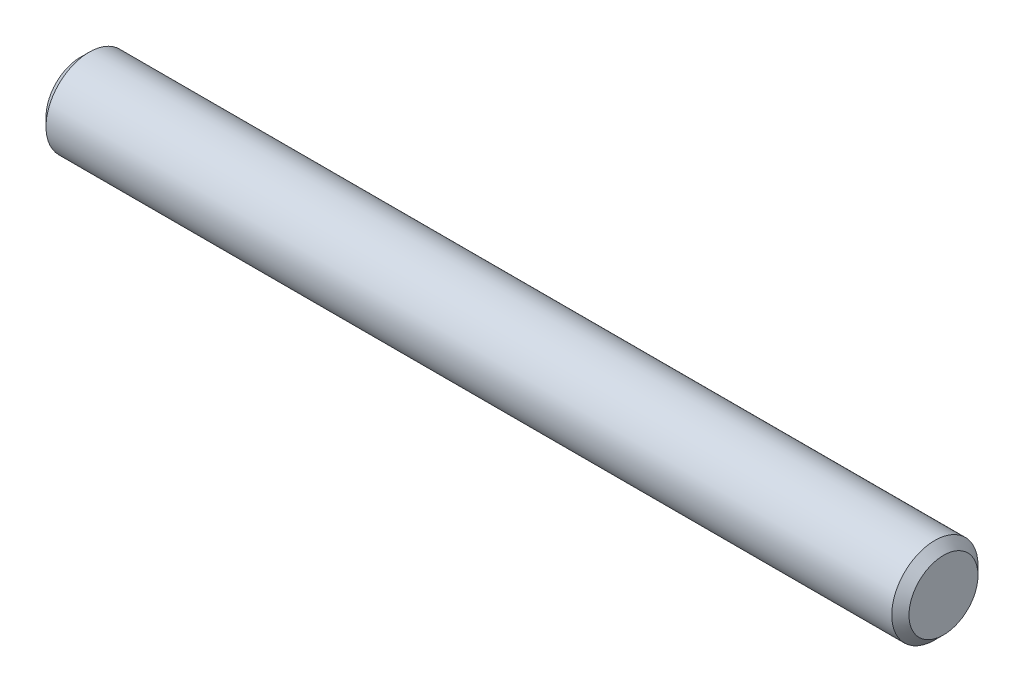
SolidWorks part; units mm, degrees
ref_plane "Front Plane" through (0, 0, 0) normal (0, 0, 1) x (1, 0, 0)
ref_plane "Top Plane" through (0, 0, 0) normal (0, 1, 0) x (1, 0, 0)
ref_plane "Right Plane" through (0, 0, 0) normal (1, 0, 0) x (0, 0, -1)
sketch "Sketch1" plane through (0, 0, 0) normal (0, 0, 1) x (1, 0, 0)
  line L0 (-31.75, 0) -> (31.75, 0) construction
  line L1 (-31.75, 3.175) -> (-31.75, -3.175) construction
  line L2 (31.75, 3.175) -> (31.75, -3.175) construction
  dimension "Diameter" = 6.35
  dimension "Length" = 63.5
sketch "Sketch2" plane through (0, 0, 0) normal (1, 0, 0) x (0, 0, -1)
  circle A0 centre (0, 0) radius 3.175
extrude "Extrude1" add sketch "Sketch2" against normal up to vertex (31.75 mm away) and the other way up to vertex (31.75 mm away) up to point (-31.75, 0, 0) other way up to point (31.75, 0, 0)
chamfer "Chamfer1" distance 0.635 angle 45 2 edges at (31.75, 0, -3.175) (-31.75, 0, -3.175)
equation "\"D1@Chamfer1\" = \"Diameter@Sketch1\"*.1"
